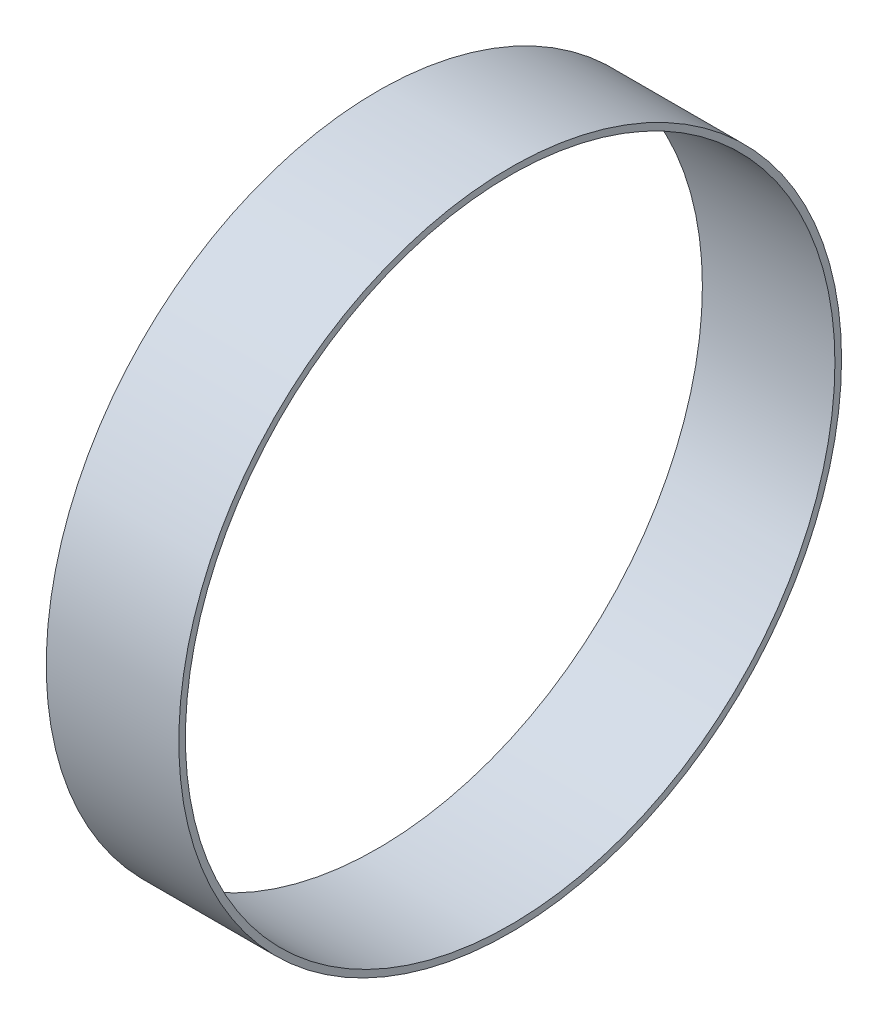
SolidWorks part; units mm, degrees
material "Elastic Band"
ref_plane "Front Plane" through (0, 0, 0) normal (0, 0, 1) x (1, 0, 0)
ref_plane "Top Plane" through (0, 0, 0) normal (0, 1, 0) x (1, 0, 0)
ref_plane "Right Plane" through (0, 0, 0) normal (1, 0, 0) x (0, 0, -1)
sketch "Sketch1" plane through (0, 0, 0) normal (1, 0, 0) x (0, 0, -1)
  circle A0 centre (0, 0) radius 24.5
  circle A1 centre (0, 0) radius 25
  dimension "D1" = 50
  dimension "D2" = 49
extrude "Boss-Extrude1" add sketch "Sketch1" along normal blind 10
